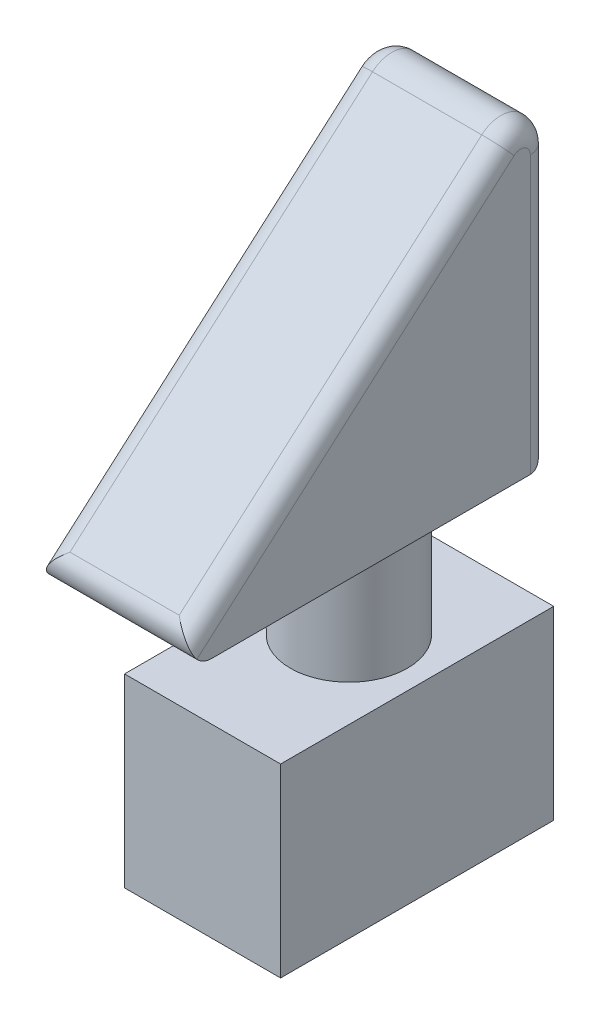
SolidWorks part; units mm, degrees
ref_plane "Front Plane" through (0, 0, 0) normal (0, 0, 1) x (1, 0, 0)
ref_plane "Top Plane" through (0, 0, 0) normal (0, 1, 0) x (1, 0, 0)
ref_plane "Right Plane" through (0, 0, 0) normal (1, 0, 0) x (0, 0, -1)
sketch "Sketch1" plane through (0, 0, 0) normal (1, 0, 0) x (0, 0, -1)
  line L0 (0, 0) -> (-40, 0)
  line L1 (-40, 0) -> (0, 35)
  line L2 (0, 35) -> (0, 0)
  dimension "D1" = 40
  dimension "D2" = 35
extrude "Boss-Extrude1" add sketch "Sketch1" along normal blind 15.2
sketch "Sketch2" plane through (0, 0, 0) normal (0, -1, 0) x (1, 0, 0)
  line L0 (15.2, 0) -> (0, 0) construction
  circle A0 centre (7.6, 13) radius 6
  point P4 (7.6, 0)
  dimension "D1" = 12
  dimension "D2" = 13
extrude "Boss-Extrude2" add sketch "Sketch2" along normal blind 12.5
sketch "Sketch3" plane through (0, -12.5, 0) normal (0, -1, 0) x (1, 0, 0)
  line L0 (15.2, 0) -> (0, 0) construction
  line L1 (-0.4, 0) -> (15.6, 0)
  line L2 (-0.4, 0) -> (-0.4, 28)
  line L3 (-0.4, 28) -> (15.6, 28)
  line L4 (15.6, 0) -> (15.6, 28)
  point P4 (7.6, 0)
  point P7 (7.6, 0)
  dimension "D1" = 16
  dimension "D2" = 28
extrude "Boss-Extrude3" add sketch "Sketch3" along normal blind 19
fillet "Fillet1" radius 3 1 edges at (7.6, 35, 0)
fillet "Fillet2" radius 2 8 edges at (15.2, 31.1206, 1.7604) (0, 31.1206, 1.7604) (7.6, 0, 0) (15.2, 14.1943, 0) (0, 14.1943, 0) (7.6, 0, 40) (15.2, 15.3232, 22.4878) (0, 15.3232, 22.4878)
